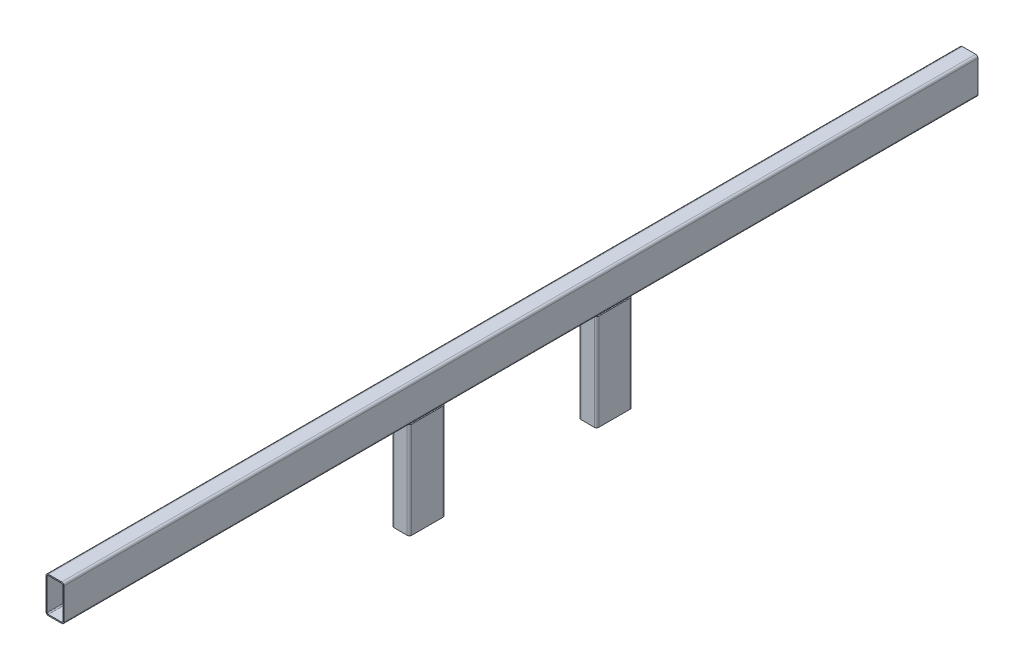
SolidWorks part; units mm, degrees
material "Plain Carbon Steel"
ref_plane "Front Plane" through (0, 0, 0) normal (0, 0, 1) x (1, 0, 0)
ref_plane "Top Plane" through (0, 0, 0) normal (0, 1, 0) x (1, 0, 0)
ref_plane "Right Plane" through (0, 0, 0) normal (1, 0, 0) x (0, 0, -1)
sketch "Sketch1" plane through (0, 0, 0) normal (1, 0, 0) x (0, 0, -1)
  line L0 (-1270, 0) -> (1270, 0)
  line L1 (-260, 0) -> (-260, -317.8116)
  line L2 (260, 0) -> (260, -317.8116)
  line L3 (-260, -158.9058) -> (260, -158.9058) construction
  line L4 (0, 0) -> (0, -158.9058) construction
  dimension "D1" = 2540
  dimension "D2" = 520
other "Structural Member1"
ref_plane "Plane1" through (0, 0, 1270) normal (0, 0, -1) x (1, 0, 0)
sketch "Sketch11" plane through (0, 0, 1270) normal (0, 0, -1) x (1, 0, 0)
  line L0 (-18.6, -46.8) -> (18.6, -46.8)
  line L1 (-21.8, -43.6) -> (-21.8, 43.6)
  line L2 (18.6, 46.8) -> (-18.6, 46.8)
  line L3 (21.8, 43.6) -> (21.8, -43.6)
  line L4 (-18.6, -50) -> (18.6, -50)
  line L5 (-25, -43.6) -> (-25, 43.6)
  line L6 (18.6, 50) -> (-18.6, 50)
  line L7 (25, 43.6) -> (25, -43.6)
  arc A0 (25, 43.6) -> (18.6, 50) centre (18.6, 43.6) ccw
  arc A1 (18.6, -50) -> (25, -43.6) centre (18.6, -43.6) ccw
  arc A2 (-25, -43.6) -> (-18.6, -50) centre (-18.6, -43.6) ccw
  arc A3 (-18.6, 50) -> (-25, 43.6) centre (-18.6, 43.6) ccw
  arc A4 (-18.6, 46.8) -> (-21.8, 43.6) centre (-18.6, 43.6) ccw
  arc A5 (21.8, 43.6) -> (18.6, 46.8) centre (18.6, 43.6) ccw
  arc A6 (18.6, -46.8) -> (21.8, -43.6) centre (18.6, -43.6) ccw
  arc A7 (-21.8, -43.6) -> (-18.6, -46.8) centre (-18.6, -43.6) ccw
  point P0 (0, 50)
  point P1 (25, 0)
  point P2 (0, -50)
  point P3 (-25, 0)
  point P4 (-25, 50)
  point P5 (25, 50)
  point P6 (25, -50)
  point P7 (-25, -50)
  point P8 (0, 0)
  point P33 (0, 0)
  dimension "D1" = 6.4
  dimension "Thickness" = 3.2
  dimension "V_leg" = 100
  dimension "H_leg" = 50
